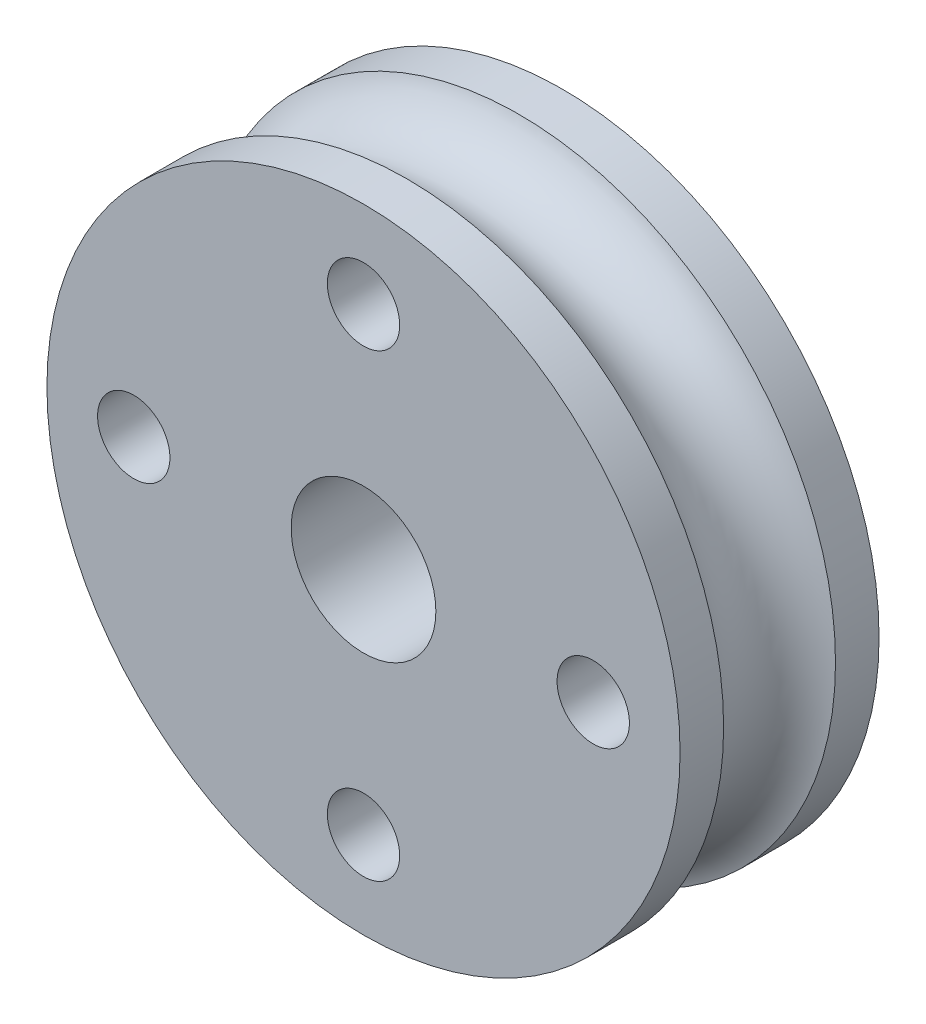
SolidWorks part; units mm, degrees
material "1060 Alloy"
ref_plane "Front Plane" through (0, 0, 0) normal (0, 0, 1) x (1, 0, 0)
ref_plane "Top Plane" through (0, 0, 0) normal (0, 1, 0) x (1, 0, 0)
ref_plane "Right Plane" through (0, 0, 0) normal (1, 0, 0) x (0, 0, -1)
sketch "Sketch1" plane through (0, 0, 0) normal (0, 0, 1) x (1, 0, 0)
  circle A0 centre (0, 0) radius 17.5
  dimension "D1" = 35
extrude "Boss-Extrude1" add sketch "Sketch1" along normal mid plane 11
sketch "Sketch2" plane through (0, 0, 0) normal (1, 0, 0) x (0, 0, -1)
  line L0 (0, 44.2539) -> (0, -44.2539) construction
  line L1 (55, 0) -> (-55, 0) construction
  line L2 (0, 0) -> (9.9966, 0) construction
  circle A0 centre (0, 18.5) radius 3.25
  dimension "D1" = 6.5
  dimension "D2" = 18.5
revolve "Cut-Revolve1" cut sketch "Sketch2" angle 360 about L2
hole_wizard "Ø8.0mm Dowel Hole1" positions "Sketch3" profile "Sketch4" hole size "Ø8.0" standard "ISO" end condition through all
sketch "Sketch3" plane through (0, 0, 5.5) normal (0, 0, 1) x (1, 0, 0)
  point P0 (0, 0)
sketch "Sketch4" plane through (0, 0, 5.5) normal (1, 0, 0) x (0, -1, 0)
  line L0 (0, 0) -> (0, 11)
  line L1 (0, 11) -> (4, 11)
  line L2 (4, 11) -> (4, 0)
  line L5 (4, 0) -> (0, 0)
  line L11 (0, -6.35) -> (0, 107.95) construction
  dimension "Thru Hole Dia." = 8
  dimension "Thru Hole Depth" = 11
hole_wizard "Ø4.0mm Dowel Hole1" positions "Sketch5" profile "Sketch6" hole size "Ø4.0" standard "ISO" end condition through all
sketch "Sketch5" plane through (0, 0, 5.5) normal (0, 0, 1) x (1, 0, 0)
  circle A0 centre (0, 0) radius 12.7
  point P0 (0, 12.7)
  point P2 (12.7, 0)
  point P4 (0, -12.7)
  point P6 (-12.7, 0)
  dimension "D1" = 25.4
sketch "Sketch6" plane through (0, 12.7, 5.5) normal (1, 0, 0) x (0, -1, 0)
  line L0 (0, 0) -> (0, 11)
  line L1 (0, 11) -> (2, 11)
  line L2 (2, 11) -> (2, 0)
  line L5 (2, 0) -> (0, 0)
  line L11 (0, -6.35) -> (0, 107.95) construction
  dimension "Thru Hole Dia." = 4
  dimension "Thru Hole Depth" = 11
